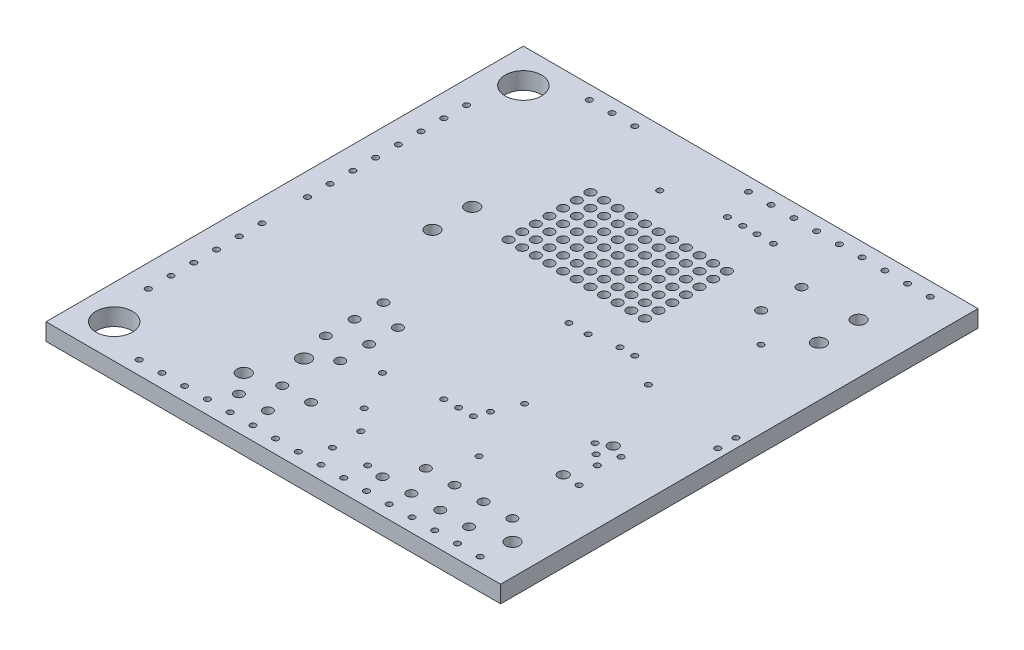
SolidWorks part; units mm, degrees
ref_plane "Front Plane" through (0, 0, 0) normal (0, 0, 1) x (1, 0, 0)
ref_plane "Top Plane" through (0, 0, 0) normal (0, 1, 0) x (1, 0, 0)
ref_plane "Right Plane" through (0, 0, 0) normal (1, 0, 0) x (0, 0, -1)
sketch "Sketch1" plane through (0, 0, 0) normal (0, 1, 0) x (1, 0, 0)
  line L1 (0, 0) -> (40, 0)
  line L2 (0, 0) -> (0, 42)
  line L3 (0, 42) -> (40, 42)
  line L4 (40, 0) -> (40, 42)
  dimension "D1" = 42
  dimension "D2" = 40
extrude "Boss-Extrude1" add sketch "Sketch1" along normal blind 1.5
sketch "Sketch3" plane through (0, 1.5, 0) normal (0, 1, 0) x (1, 0, 0)
  circle A0 centre (37.0001, 1.1992) radius 0.254
  circle A1 centre (34.9986, 1.1992) radius 0.254
  circle A2 centre (32.9996, 1.1992) radius 0.254
  circle A3 centre (31.0006, 1.1992) radius 0.254
  circle A4 centre (28.9991, 1.1992) radius 0.254
  circle A5 centre (27.0001, 1.1992) radius 0.254
  circle A6 centre (24.9986, 1.1992) radius 0.254
  circle A7 centre (22.9996, 1.1992) radius 0.254
  circle A8 centre (22.1995, 3.0001) radius 0.254
  circle A9 centre (21.0006, 1.1992) radius 0.254
  circle A10 centre (18.9991, 1.1992) radius 0.254
  circle A11 centre (17.0001, 1.1992) radius 0.254
  circle A12 centre (14.9986, 1.1992) radius 0.254
  circle A13 centre (12.9996, 1.1992) radius 0.254
  circle A14 centre (11.0007, 1.1992) radius 0.254
  circle A15 centre (8.9991, 1.1992) radius 0.254
  circle A16 centre (7.0002, 1.1992) radius 0.254
  circle A17 centre (1.9989, 7.0006) radius 0.254
  circle A18 centre (1.9989, 8.9995) radius 0.254
  circle A19 centre (1.9989, 11.0011) radius 0.254
  circle A20 centre (1.9989, 13) radius 0.254
  circle A21 centre (1.9989, 15.0016) radius 0.254
  circle A22 centre (1.9989, 17.0005) radius 0.254
  circle A23 centre (1.9989, 21.001) radius 0.254
  circle A24 centre (1.9989, 23) radius 0.254
  circle A25 centre (1.9989, 25.0015) radius 0.254
  circle A26 centre (1.9989, 27.0005) radius 0.254
  circle A27 centre (1.9989, 28.9995) radius 0.254
  circle A28 centre (1.9989, 31.001) radius 0.254
  circle A29 centre (1.9989, 33) radius 0.254
  circle A30 centre (1.9989, 35.0015) radius 0.254
  circle A31 centre (7.0002, 40.8003) radius 0.254
  circle A32 centre (8.9991, 40.8003) radius 0.254
  circle A33 centre (11.0007, 40.8003) radius 0.254
  circle A34 centre (17.0001, 37.0005) radius 0.254
  circle A35 centre (21.0006, 40.8003) radius 0.254
  circle A36 centre (22.9996, 40.8003) radius 0.254
  circle A37 centre (24.9986, 40.8003) radius 0.254
  circle A38 centre (27.0001, 40.8003) radius 0.254
  circle A39 centre (28.9991, 40.8003) radius 0.254
  circle A40 centre (31.0006, 40.8003) radius 0.254
  circle A41 centre (32.9996, 40.8003) radius 0.254
  circle A42 centre (34.9986, 40.8003) radius 0.254
  circle A43 centre (37.0001, 40.8003) radius 0.254
  circle A44 centre (26.0502, 37.9505) radius 0.254
  circle A45 centre (24.5998, 37.9505) radius 0.254
  circle A46 centre (23.3501, 37.9505) radius 0.254
  circle A47 centre (21.9989, 37.9505) radius 0.254
  circle A48 centre (33.2003, 29.7005) radius 0.254
  circle A49 centre (28.4987, 23.2997) radius 0.254
  circle A50 centre (27.2008, 23.2997) radius 0.254
  circle A51 centre (24.8005, 22.901) radius 0.254
  circle A52 centre (23.0987, 22.901) radius 0.254
  circle A53 centre (31.3003, 21.6995) radius 0.254
  circle A54 centre (33.3984, 14.9) radius 0.254
  circle A55 centre (34.3001, 14.0999) radius 0.254
  circle A56 centre (35.1992, 13.2998) radius 0.254
  circle A57 centre (35.6006, 15.0016) radius 0.254
  circle A58 centre (35.9003, 11.0011) radius 0.254
  circle A59 centre (29.2988, 8.8014) radius 0.254
  circle A60 centre (25.9994, 11.6005) radius 0.254
  circle A61 centre (26.4007, 12.7003) radius 0.254
  circle A62 centre (24.6989, 11.6005) radius 0.254
  circle A63 centre (23.3984, 11.6005) radius 0.254
  circle A64 centre (27.2998, 14.8009) radius 0.254
  circle A65 centre (20.5993, 7.3993) radius 0.254
  circle A66 centre (22.1995, 5.4994) radius 0.254
  circle A67 centre (25.1002, 3.2007) radius 0.254
  circle A68 centre (18.6994, 10.8995) radius 0.254
  circle A69 centre (39.1997, 19.9012) radius 0.254
  circle A70 centre (39.1997, 21.5014) radius 0.254
  circle A71 centre (26.0984, 26.5992) radius 0.4064
  circle A72 centre (26.0984, 27.8006) radius 0.4064
  circle A73 centre (24.8995, 27.8006) radius 0.4064
  circle A74 centre (24.8995, 26.5992) radius 0.4064
  circle A75 centre (23.7007, 26.5992) radius 0.4064
  circle A76 centre (23.7007, 27.8006) radius 0.4064
  circle A77 centre (23.7007, 28.9995) radius 0.4064
  circle A78 centre (24.8995, 28.9995) radius 0.4064
  circle A79 centre (26.0984, 28.9995) radius 0.4064
  circle A80 centre (26.0984, 30.2009) radius 0.4064
  circle A81 centre (24.8995, 30.2009) radius 0.4064
  circle A82 centre (24.8995, 31.3998) radius 0.4064
  circle A83 centre (23.7007, 31.3998) radius 0.4064
  circle A84 centre (23.7007, 30.2009) radius 0.4064
  circle A85 centre (22.4992, 30.2009) radius 0.4064
  circle A86 centre (21.3004, 30.2009) radius 0.4064
  circle A87 centre (21.3004, 31.3998) radius 0.4064
  circle A88 centre (22.4992, 31.3998) radius 0.4064
  circle A89 centre (22.4992, 32.6012) radius 0.4064
  circle A90 centre (22.4992, 33.8001) radius 0.4064
  circle A91 centre (21.3004, 33.8001) radius 0.4064
  circle A92 centre (21.3004, 32.6012) radius 0.4064
  circle A93 centre (20.0989, 32.6012) radius 0.4064
  circle A94 centre (20.0989, 33.8001) radius 0.4064
  circle A95 centre (18.9001, 33.8001) radius 0.4064
  circle A96 centre (18.9001, 32.6012) radius 0.4064
  circle A97 centre (17.6986, 32.6012) radius 0.4064
  circle A98 centre (17.6986, 33.8001) radius 0.4064
  circle A99 centre (16.4998, 33.8001) radius 0.4064
  circle A100 centre (16.4998, 32.6012) radius 0.4064
  circle A101 centre (15.2983, 32.6012) radius 0.4064
  circle A102 centre (14.0995, 32.6012) radius 0.4064
  circle A103 centre (14.0995, 33.8001) radius 0.4064
  circle A104 centre (15.2983, 33.8001) radius 0.4064
  circle A105 centre (15.2983, 31.3998) radius 0.4064
  circle A106 centre (14.0995, 31.3998) radius 0.4064
  circle A107 centre (14.0995, 30.2009) radius 0.4064
  circle A108 centre (15.2983, 30.2009) radius 0.4064
  circle A109 centre (15.2983, 28.9995) radius 0.4064
  circle A110 centre (14.0995, 28.9995) radius 0.4064
  circle A111 centre (14.0995, 27.8006) radius 0.4064
  circle A112 centre (15.2983, 27.8006) radius 0.4064
  circle A113 centre (15.2983, 26.5992) radius 0.4064
  circle A114 centre (14.0995, 26.5992) radius 0.4064
  circle A115 centre (16.4998, 26.5992) radius 0.4064
  circle A116 centre (16.4998, 27.8006) radius 0.4064
  circle A117 centre (17.6986, 27.8006) radius 0.4064
  circle A118 centre (17.6986, 26.5992) radius 0.4064
  circle A119 centre (18.9001, 26.5992) radius 0.4064
  circle A120 centre (18.9001, 27.8006) radius 0.4064
  circle A121 centre (20.0989, 27.8006) radius 0.4064
  circle A122 centre (20.0989, 26.5992) radius 0.4064
  circle A123 centre (21.3004, 26.5992) radius 0.4064
  circle A124 centre (22.4992, 26.5992) radius 0.4064
  circle A125 centre (22.4992, 27.8006) radius 0.4064
  circle A126 centre (21.3004, 27.8006) radius 0.4064
  circle A127 centre (21.3004, 28.9995) radius 0.4064
  circle A128 centre (22.4992, 28.9995) radius 0.4064
  circle A129 centre (20.0989, 28.9995) radius 0.4064
  circle A130 centre (18.9001, 28.9995) radius 0.4064
  circle A131 centre (17.6986, 28.9995) radius 0.4064
  circle A132 centre (16.4998, 28.9995) radius 0.4064
  circle A133 centre (16.4998, 30.2009) radius 0.4064
  circle A134 centre (16.4998, 31.3998) radius 0.4064
  circle A135 centre (17.6986, 31.3998) radius 0.4064
  circle A136 centre (17.6986, 30.2009) radius 0.4064
  circle A137 centre (18.9001, 30.2009) radius 0.4064
  circle A138 centre (20.0989, 30.2009) radius 0.4064
  circle A139 centre (20.0989, 31.3998) radius 0.4064
  circle A140 centre (18.9001, 31.3998) radius 0.4064
  circle A141 centre (23.7007, 32.6012) radius 0.4064
  circle A142 centre (23.7007, 33.8001) radius 0.4064
  circle A143 centre (24.8995, 33.8001) radius 0.4064
  circle A144 centre (24.8995, 32.6012) radius 0.4064
  circle A145 centre (26.0984, 32.6012) radius 0.4064
  circle A146 centre (26.0984, 33.8001) radius 0.4064
  circle A147 centre (26.0984, 31.3998) radius 0.4064
  circle A148 centre (30.5993, 32.3218) radius 0.4064
  circle A149 centre (30.5993, 35.8778) radius 0.4064
  circle A150 centre (13.3908, 16.3046) radius 0.4064
  circle A151 centre (13.3908, 13.7646) radius 0.4064
  circle A152 centre (13.3908, 11.2246) radius 0.4064
  circle A153 centre (15.9308, 9.9546) radius 0.4064
  circle A154 centre (15.9308, 12.4946) radius 0.4064
  circle A155 centre (15.9308, 15.0346) radius 0.4064
  circle A156 centre (15.2653, 5.5197) radius 0.4064
  circle A157 centre (17.8053, 5.5197) radius 0.4064
  circle A158 centre (16.5353, 2.9797) radius 0.4064
  circle A159 centre (13.9953, 2.9797) radius 0.4064
  circle A160 centre (26.614, 2.9899) radius 0.4064
  circle A161 centre (29.154, 2.9899) radius 0.4064
  circle A162 centre (31.694, 2.9899) radius 0.4064
  circle A163 centre (34.234, 2.9899) radius 0.4064
  circle A164 centre (32.964, 5.5299) radius 0.4064
  circle A165 centre (30.424, 5.5299) radius 0.4064
  circle A166 centre (27.884, 5.5299) radius 0.4064
  circle A167 centre (35.504, 5.5299) radius 0.4064
  circle A168 centre (34.4195, 11.09) radius 0.4445
  circle A169 centre (34.4195, 15.4892) radius 0.4445
  circle A170 centre (37.2998, 3.7494) radius 0.5969
  circle A171 centre (14.1503, 8.55) radius 0.5969
  circle A172 centre (12.5983, 4.8009) radius 0.5969
  circle A173 centre (9.9999, 24.0008) radius 0.5969
  circle A174 centre (9.9999, 27.5009) radius 0.5969
  circle A175 centre (35.6006, 32.4006) radius 0.5969
  circle A176 centre (35.6006, 35.9007) radius 0.5969
  circle A177 centre (2.9997, 38.9995) radius 1.6002
  circle A178 centre (2.9997, 3.0001) radius 1.6002
extrude "Cut-Extrude1" cut sketch "Sketch3" against normal up to next (1.5 mm away)
